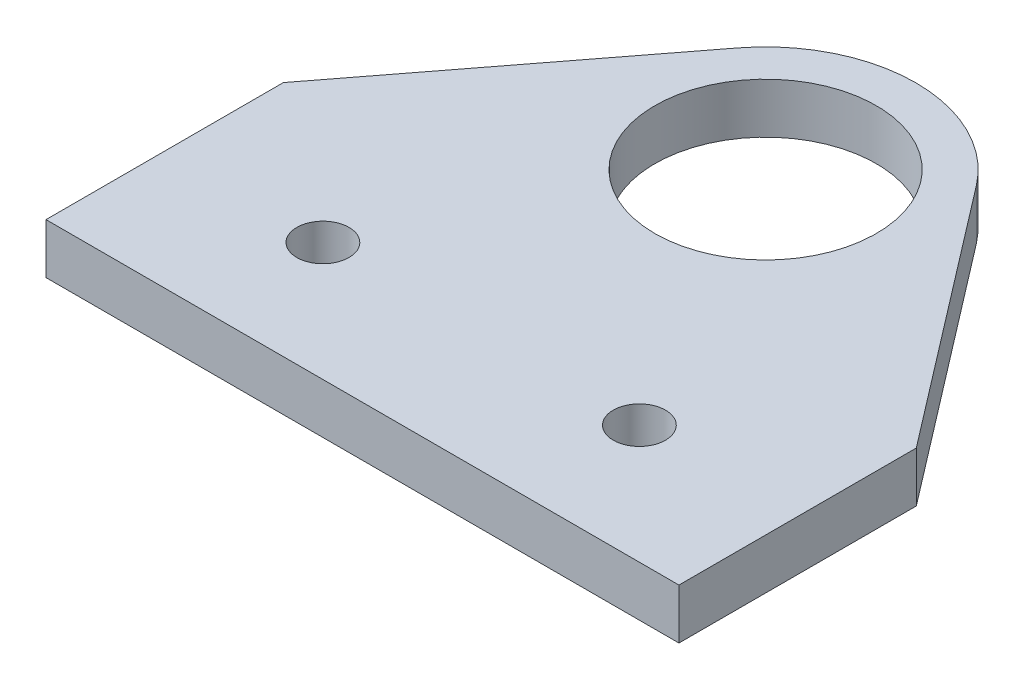
SolidWorks part; units mm, degrees
ref_plane "Front" through (0, 0, 0) normal (0, 0, 1) x (1, 0, 0)
ref_plane "Top" through (0, 0, 0) normal (0, 1, 0) x (1, 0, 0)
ref_plane "Right" through (0, 0, 0) normal (1, 0, 0) x (0, 0, -1)
sketch "Sketch1" plane through (0, 0, 0) normal (0, 1, 0) x (1, 0, 0)
  line L0 (-40, 15) -> (-15.0792, 47.5093)
  line L1 (-40, -15) -> (40, -15)
  line L2 (-40, -15) -> (-40, 15)
  line L3 (-40, 15) -> (40, 15)
  line L4 (40, -15) -> (40, 15)
  line L5 (0, 15) -> (0, -15) construction
  line L6 (-40, 0) -> (40, 0) construction
  line L7 (40, 15) -> (15.0792, 47.5093)
  circle A0 centre (0, 35.95) radius 19
  circle A1 centre (0, 35.95) radius 14
  point P0 (0, 0)
  dimension "D3" = 35.95
  dimension "D4" = 38
  dimension "D5" = 28
  dimension "D1" = 80
  dimension "D2" = 30
extrude "Boss-Extrude1" add sketch "Sketch1" along normal blind 6.35 contours L1 L4 L3 L2 | A0 L0 L3 L7 | A0
hole_wizard "M6 Clearance Hole1" positions "Sketch3" profile "Sketch2" hole size "M6" standard "ANSI Metric" end condition through all
sketch "Sketch3" plane through (0, 6.35, 0) normal (0, 1, 0) x (1, 0, 0)
  point P0 (-20, 0)
  point P2 (20, 0)
  dimension "D1" = 20
  dimension "D2" = 20
sketch "Sketch2" plane through (-20, 6.35, 0) normal (1, 0, 0) x (0, 0, 1)
  line L0 (0, 0) -> (0, 6.35)
  line L1 (0, 6.35) -> (3.3, 6.35)
  line L2 (3.3, 6.35) -> (3.3, 0)
  line L5 (3.3, 0) -> (0, 0)
  line L11 (0, -6.35) -> (0, 107.95) construction
  dimension "Thru Hole Dia." = 6.6
  dimension "Thru Hole Depth" = 6.35
